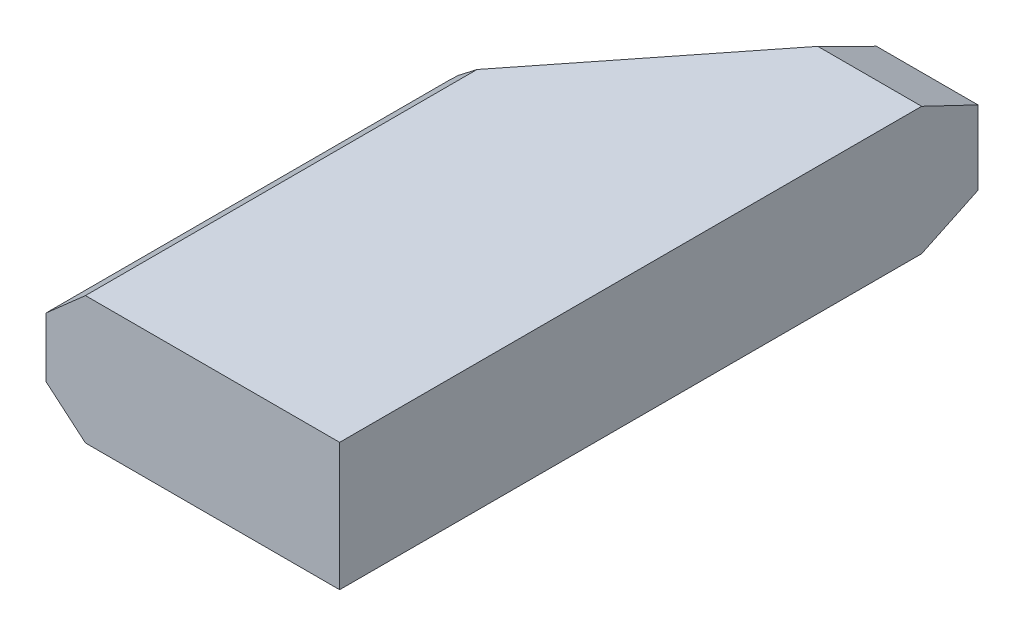
SolidWorks part; units mm, degrees
ref_plane "Front Plane" through (0, 0, 0) normal (0, 0, 1) x (1, 0, 0)
ref_plane "Top Plane" through (0, 0, 0) normal (0, 1, 0) x (1, 0, 0)
ref_plane "Right Plane" through (0, 0, 0) normal (1, 0, 0) x (0, 0, -1)
sketch "Sketch1" plane through (0, 0, 0) normal (0, 0, 1) x (1, 0, 0)
  line L1 (0, 0) -> (-233.68, 0)
  line L2 (0, 0) -> (0, 101.6)
  line L3 (0, 101.6) -> (-233.68, 101.6)
  line L4 (-233.68, 0) -> (-233.68, 101.6)
extrude "Boss-Extrude1" add sketch "Sketch1" against normal blind 508
sketch "Sketch2" plane through (0, 0, 0) normal (0, 0, 1) x (1, 0, 0)
  line L0 (-202.2835, 101.6) -> (-233.68, 73.9081)
  line L1 (0, 101.6) -> (-233.68, 101.6) construction
  line L2 (-233.68, 101.6) -> (-233.68, 0) construction
  line L3 (-233.68, 73.9081) -> (-233.68, 101.6)
  line L4 (-233.68, 101.6) -> (-202.2835, 101.6)
  line L5 (-202.2835, 0) -> (-233.68, 26.611)
  line L6 (-233.68, 0) -> (0, 0) construction
  line L7 (-233.68, 26.611) -> (-233.68, 0)
  line L8 (-233.68, 0) -> (-202.2835, 0)
extrude "Cut-Extrude1" cut sketch "Sketch2" against normal through all
sketch "Sketch3" plane through (0, 101.6, 0) normal (0, 1, 0) x (1, 0, 0)
  line L0 (-87.0708, 508) -> (-233.68, 321.5857)
  line L1 (0, 508) -> (-202.2835, 508) construction
  line L2 (-233.68, 508) -> (-233.68, 0) construction
  line L3 (-233.68, 321.5857) -> (-233.68, 508)
  line L4 (-233.68, 508) -> (-87.0708, 508)
extrude "Cut-Extrude2" cut sketch "Sketch3" against normal through all
sketch "Sketch4" plane through (0, 0, 0) normal (1, 0, 0) x (0, 0, -1)
  line L0 (463.1616, 101.6) -> (508, 80.1575)
  line L1 (508, 101.6) -> (0, 101.6) construction
  line L2 (508, 0) -> (508, 101.6) construction
  line L3 (508, 80.1575) -> (508, 101.6)
  line L4 (508, 101.6) -> (463.1616, 101.6)
  line L5 (463.1616, 0) -> (508, 21.3199)
  line L6 (508, 0) -> (0, 0) construction
  line L7 (508, 21.3199) -> (508, 0)
  line L8 (508, 0) -> (463.1616, 0)
extrude "Cut-Extrude3" cut sketch "Sketch4" against normal through all
sketch "Sketch5" plane through (217.2058, 0, -275.1273) normal (0.6196, 0, -0.7849) x (-0.7849, 0, -0.6196)
  line L0 (351.8627, 101.6) -> (383.1196, 76.1756)
  line L1 (383.0139, 101.6) -> (286.9955, 101.6) construction
  line L2 (383.1196, 21.3199) -> (383.1196, 80.1575) construction
  line L3 (383.1196, 76.1756) -> (383.0139, 101.6)
  line L4 (383.0139, 101.6) -> (351.8627, 101.6)
  line L5 (383.1196, 27.6342) -> (351.8627, 0)
  line L6 (383.0139, 0) -> (286.9955, 0) construction
  line L7 (351.8627, 0) -> (383.0139, 0)
  line L8 (383.1196, 21.3199) -> (383.0139, 0) construction
  line L9 (383.0139, 0) -> (383.1196, 27.6342)
  line L10 (351.8627, 101.6) -> (351.8627, 0) construction
extrude "Cut-Extrude4" cut sketch "Sketch5" against normal through all
